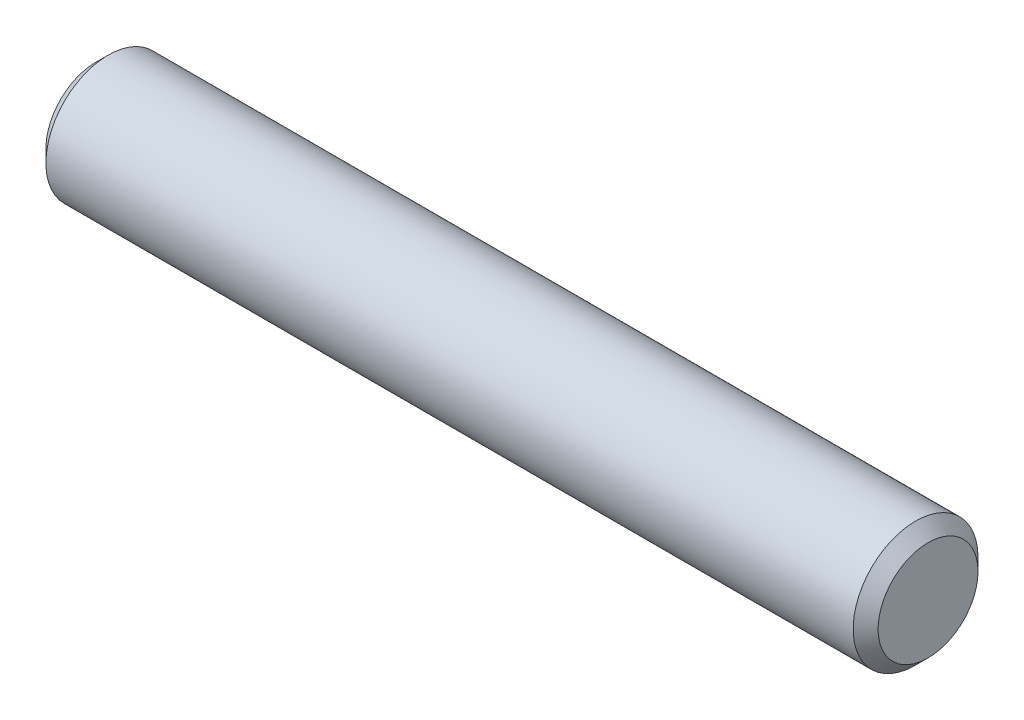
SolidWorks part; units mm, degrees
material "Alloy Steel"
ref_plane "Front" through (0, 0, 0) normal (0, 0, 1) x (1, 0, 0)
ref_plane "Top" through (0, 0, 0) normal (0, 1, 0) x (1, 0, 0)
ref_plane "Right" through (0, 0, 0) normal (1, 0, 0) x (0, 0, -1)
sketch "Sketch1" plane through (0, 0, 0) normal (0, 0, 1) x (1, 0, 0)
  line L0 (-7.9375, 0) -> (7.9375, 0) construction
  line L1 (7.9375, 1.1906) -> (7.9375, -1.1906) construction
  line L2 (-7.9375, 1.1906) -> (-7.9375, -1.1906) construction
  dimension "Length" = 15.875
  dimension "Diameter" = 2.3813
sketch "Sketch2" plane through (0, 0, 0) normal (1, 0, 0) x (0, 0, -1)
  circle A0 centre (0, 0) radius 1.1906
extrude "Extrude1" add sketch "Sketch2" against normal up to vertex (7.9375 mm away) and the other way up to vertex (7.9375 mm away) up to point (-7.9375, 1.1906, 0) other way up to point (7.9375, 1.1906, 0)
chamfer "Chamfer1" distance 0.2381 angle 45 2 edges at (7.9375, 0, -1.1906) (-7.9375, 0, -1.1906)
equation "\"D1@Chamfer1\" = \"Diameter@Sketch1\"*.1"
